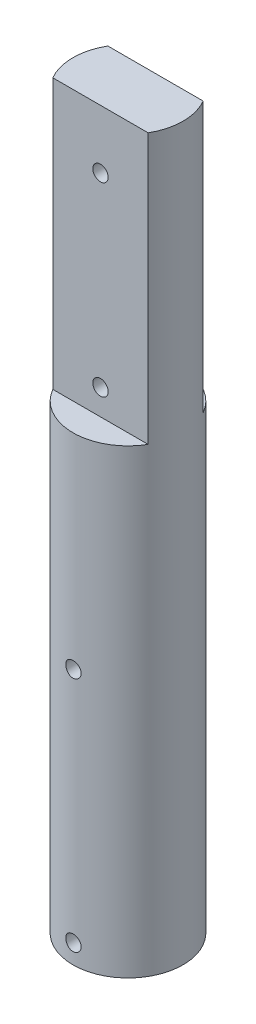
SolidWorks part; units mm, degrees
ref_plane "Front Plane" through (0, 0, 0) normal (0, 0, 1) x (1, 0, 0)
ref_plane "Top Plane" through (0, 0, 0) normal (0, 1, 0) x (1, 0, 0)
ref_plane "Right Plane" through (0, 0, 0) normal (1, 0, 0) x (0, 0, -1)
sketch "Sketch1" plane through (0, 0, 0) normal (0, 1, 0) x (1, 0, 0)
  line L0 (-4.3, 4.3) -> (4.3, 4.3)
  line L1 (-4.5, -4.5) -> (4.5, -4.5) construction
  line L2 (-4.5, -4.5) -> (-4.5, 4.5) construction
  line L3 (-4.5, 4.5) -> (4.5, 4.5) construction
  line L4 (4.5, -4.5) -> (4.5, 4.5) construction
  line L5 (4.3, -4.3) -> (4.3, 4.3)
  line L6 (-4.3, -4.3) -> (4.3, -4.3)
  line L7 (-4.3, -4.3) -> (-4.3, 4.3)
  point P0 (0, 0)
  dimension "D1" = 9
  dimension "D2" = 9
  dimension "D3" = 0.2
sketch "Sketch2" plane through (0, 0, 0) normal (0, 1, 0) x (1, 0, 0)
  circle A0 centre (0, 0) radius 4.3
extrude "Boss-Extrude2" add sketch "Sketch2" along normal blind 57.08
sketch "Sketch4" plane through (0, 57.08, 0) normal (0, 1, 0) x (1, 0, 0)
  line L0 (0, 4.3) -> (0, 0) construction
  line L1 (-4.3, 0) -> (4.3, 0) construction
  line L2 (0, 2.15) -> (-3.7239, 2.15)
  line L3 (0, 2.15) -> (3.7239, 2.15)
  line L4 (0, -2.15) -> (-3.7239, -2.15)
  line L5 (0, -2.15) -> (3.7239, -2.15)
  circle A1 centre (0, 0) radius 4.3 construction
  arc A2 (-3.7239, 2.15) -> (3.7239, 2.15) centre (0, 0) cw
  arc A3 (-3.7239, -2.15) -> (3.7239, -2.15) centre (0, 0) ccw
extrude "Cut-Extrude2" cut sketch "Sketch4" against normal blind 21.08
sketch "Sketch5" plane through (0, 57.08, 0) normal (0, 1, 0) x (1, 0, 0)
  line L2 (-3.7239, -2.15) -> (3.7239, -2.15)
  line L3 (3.7239, 2.15) -> (-3.7239, 2.15)
  line L4 (-3.7239, -2.15) -> (3.7239, -2.15)
  line L5 (3.7239, 2.15) -> (-3.7239, 2.15)
  arc A2 (3.7239, -2.15) -> (3.7239, 2.15) centre (0, 0) ccw
  arc A3 (-3.7239, 2.15) -> (-3.7239, -2.15) centre (0, 0) ccw
  arc A4 (3.7239, -2.15) -> (3.7239, 2.15) centre (0, 0) ccw
  arc A5 (-3.7239, 2.15) -> (-3.7239, -2.15) centre (0, 0) ccw
  dimension "D1" = 0
sketch "Sketch6" plane through (0, 0, 0) normal (0, 0, 1) x (1, 0, 0)
  line L0 (0, 0) -> (0, 3) construction
  circle A0 centre (0, 1.5) radius 0.6
extrude "Cut-Extrude3" cut sketch "Sketch6" against normal through all both and the other way through all
sketch "Sketch7" plane through (0, 0, 2.15) normal (0, 0, 1) x (1, 0, 0)
  line L0 (0, 36) -> (0, 38) construction
  line L1 (3.7239, 36) -> (-3.7239, 36) construction
  circle A0 centre (0, 38) radius 0.6
  dimension "D1" = 2
extrude "Cut-Extrude4" cut sketch "Sketch7" against normal blind 10
sketch "Sketch8" plane through (0, 0, 0) normal (0, 0, 1) x (1, 0, 0)
  line L0 (0, 38) -> (0, 20) construction
  circle A0 centre (0, 20) radius 0.6
  dimension "D1" = 18
extrude "Cut-Extrude5" cut sketch "Sketch8" against normal through all both and the other way through all
sketch "Sketch9" plane through (0, 0, 2.15) normal (0, 0, 1) x (1, 0, 0)
  line L0 (0, 38) -> (0, 52.5) construction
  circle A0 centre (0, 52.5) radius 0.6
  dimension "D1" = 14.5
extrude "Cut-Extrude6" cut sketch "Sketch9" against normal through all
